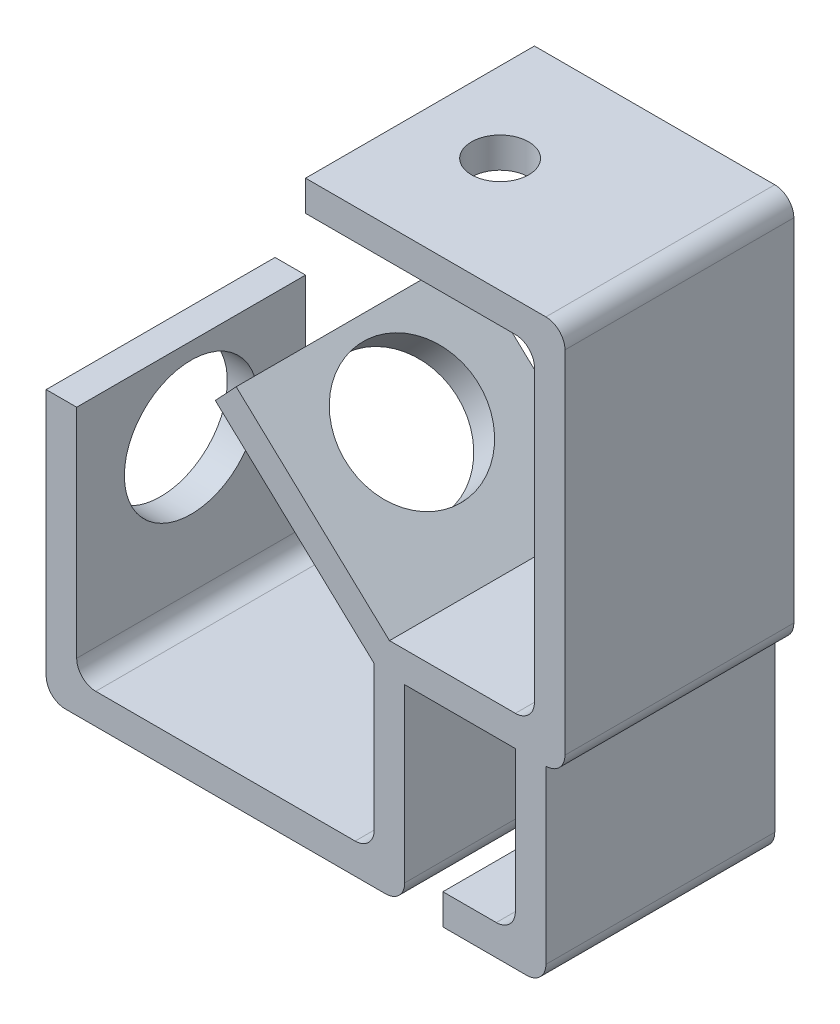
SolidWorks part; units mm, degrees
material "Gray Cast Iron (SN)"
ref_plane "Front Plane" through (0, 0, 0) normal (0, 0, 1) x (1, 0, 0)
ref_plane "Top Plane" through (0, 0, 0) normal (0, 1, 0) x (1, 0, 0)
ref_plane "Right Plane" through (0, 0, 0) normal (1, 0, 0) x (0, 0, -1)
sketch "Sketch3" plane through (0, 0, 0) normal (0, 0, 1) x (1, 0, 0)
  line L3 (0, 0) -> (-41.6509, 38.9127)
  line L4 (-41.6509, 38.9127) -> (-36.1895, 44.7585)
  line L5 (-36.1895, 44.7585) -> (4, 7.2111)
  line L10 (0, 0) -> (0, -37.7889)
  line L11 (8, -0.7889) -> (8, -45.7889)
  line L12 (3, -50.7889) -> (-86, -50.7889)
  line L13 (-5, -42.7889) -> (-78, -42.7889)
  line L14 (-78, -42.7889) -> (-78, 19.2111)
  line L15 (-86, -50.7889) -> (-86, 19.2111)
  line L16 (-86, 19.2111) -> (-78, 19.2111)
  line L36 (45, 101.2111) -> (-18, 101.2111)
  line L37 (-18, 101.2111) -> (-18, 93.2111)
  line L38 (-18, 93.2111) -> (37, 93.2111)
  line L39 (42, 88.2111) -> (42, 12.2111)
  line L40 (37, 7.2111) -> (4, 7.2111)
  line L41 (50, 96.2111) -> (50, 4.2111)
  line L42 (40, -50.7889) -> (18, -50.7889)
  line L43 (18, -50.7889) -> (18, -42.7889)
  line L44 (18, -42.7889) -> (32, -42.7889)
  line L45 (37, -37.7889) -> (37, -0.7889)
  line L46 (8, -0.7889) -> (37, -0.7889)
  line L47 (45, -0.7889) -> (45, -45.7889)
  arc A0 (0, -37.7889) -> (-5, -42.7889) centre (-5, -37.7889) cw
  arc A1 (8, -45.7889) -> (3, -50.7889) centre (3, -45.7889) cw
  arc A2 (50, 96.2111) -> (45, 101.2111) centre (45, 96.2111) ccw
  arc A3 (37, 93.2111) -> (42, 88.2111) centre (37, 88.2111) cw
  arc A4 (45, -45.7889) -> (40, -50.7889) centre (40, -45.7889) cw
  arc A5 (32, -42.7889) -> (37, -37.7889) centre (32, -37.7889) ccw
  arc A7 (42, 12.2111) -> (37, 7.2111) centre (37, 12.2111) cw
  arc A8 (50, 4.2111) -> (45, -0.7889) centre (45, 4.2111) cw
  point P22 (8, -50.7889)
  dimension "D15" = 5
  dimension "D16" = 5
  dimension "D17" = 22
  dimension "D18" = 5
  dimension "D21" = 29
  dimension "D26" = 152
  dimension "D27" = 8
  dimension "D20" = 5
  dimension "D4" = 5
  dimension "D24" = 4
  dimension "D1" = 50
  dimension "D2" = 8
  dimension "D3" = 8
  dimension "D5" = 8
  dimension "D6" = 33
  dimension "D7" = 8
  dimension "D8" = 57
  dimension "D9" = 55
  dimension "D10" = 8
  dimension "D11" = 8
  dimension "D12" = 70
  dimension "D13" = 94
  dimension "D14" = 8
  dimension "D22" = 63
  dimension "D23" = 55
  dimension "D25" = 37
extrude "Boss-Extrude3" add sketch "Sketch3" along normal mid plane 60
sketch "Sketch10" plane through (0, 0, 0) normal (-0.6827, -0.7307, 0) x (0, 0, 1)
  line L0 (-27.1909, 35) -> (115.1706, 35) construction
  line L1 (0, 159.6527) -> (0, 75.9568) construction
  line L2 (30, 75.9568) -> (-30, 75.9568) construction
  circle A0 centre (0, 35) radius 17.5
  dimension "D1" = 35
extrude "Cut-Extrude1" cut sketch "Sketch10" against normal up to surface (8 mm away) up to face at (-16.0947, 25.9848, 0)
sketch "Sketch11" plane through (-86, 0, 0) normal (-1, 0, 0) x (0, 0, 1)
  line L0 (-30, -15.4502) -> (30, -15.4502) construction
  line L3 (0, 19.5498) -> (0, -50.4502) construction
  circle A0 centre (0, -2.6) radius 17.5
  point P4 (0, 0)
  dimension "D1" = 2.6
  dimension "D2" = 35
extrude "Cut-Extrude2" cut sketch "Sketch11" against normal up to surface (8 mm away) contours A0 up to face at (-78, -11.7889, 0)
fillet "Fillet3" radius 5 1 edges at (-78, -42.7889, 0)
fillet "Fillet4" radius 5 1 edges at (-86, -50.7889, 0)
sketch "Sketch12" plane through (0, 101.2111, 0) normal (0, 1, 0) x (1, 0, 0)
  line L0 (45, 30) -> (-18, 30) construction
  line L1 (45, -30) -> (45, 30) construction
  circle A0 centre (3, 0) radius 7.5
  dimension "D1" = 15
  dimension "D2" = 42
  dimension "D3" = 30
extrude "Cut-Extrude3" cut sketch "Sketch12" against normal blind 10
